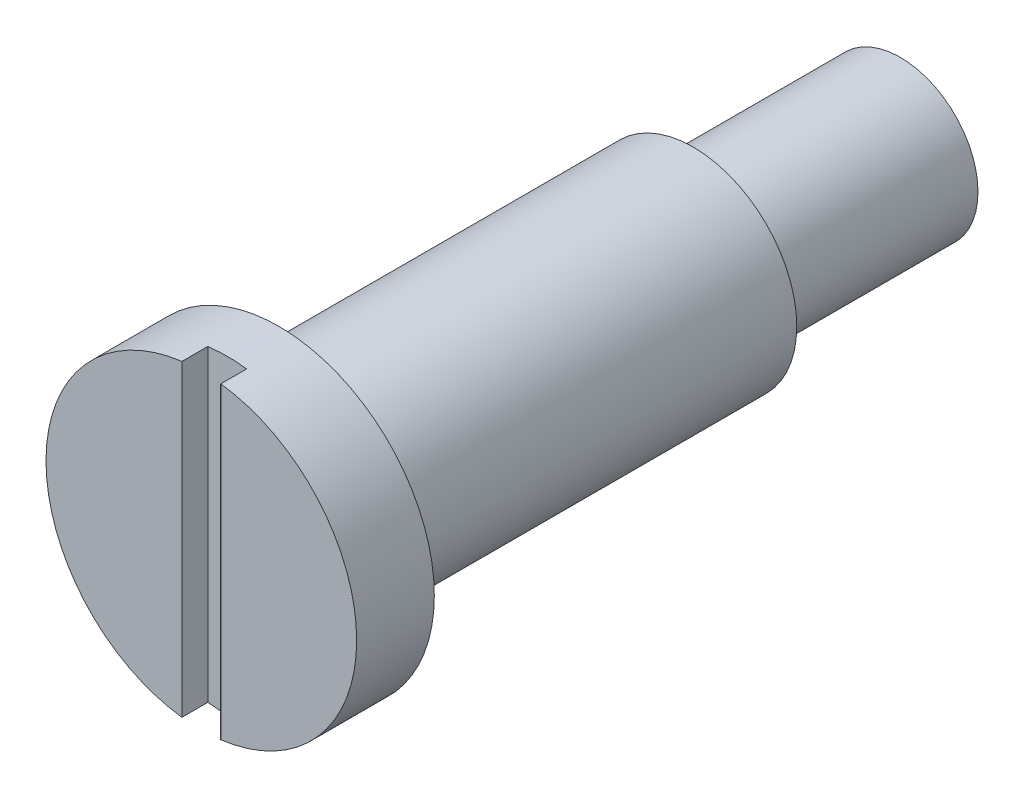
SolidWorks part; units mm, degrees
ref_plane "前视基准面" through (0, 0, 0) normal (0, 0, 1) x (1, 0, 0)
ref_plane "上视基准面" through (0, 0, 0) normal (0, 1, 0) x (1, 0, 0)
ref_plane "右视基准面" through (0, 0, 0) normal (1, 0, 0) x (0, 0, -1)
sketch "草图2" plane through (0, 0, 0) normal (1, 0, 0) x (0, 0, -1)
  line L0 (0, 0) -> (105.7683, 0) construction
  line L1 (0, 0) -> (0, 6)
  line L2 (0, 6) -> (3, 6)
  line L3 (3, 6) -> (3, 4)
  line L4 (3, 4) -> (19, 4)
  line L5 (19, 4) -> (19, 3)
  line L6 (0, 0) -> (27, 0)
  line L7 (19, 3) -> (27, 3)
  line L8 (27, 3) -> (27, 0)
  dimension "D1" = 12
  dimension "D2" = 16
  dimension "D3" = 3
  dimension "D4" = 8
  dimension "D5" = 6
  dimension "D6" = 8
revolve "旋转1" add sketch "草图2" angle 360 about L0
cosmetic thread "装饰螺纹线1"
sketch "草图3" plane through (0, 0, 0) normal (0, 0, 1) x (1, 0, 0)
  line L0 (0, 6) -> (0, -6) construction
  line L2 (-0.75, 6) -> (0.75, 6)
  line L3 (-0.75, 6) -> (-0.75, -6)
  line L4 (-0.75, -6) -> (0.75, -6)
  line L5 (0.75, 6) -> (0.75, -6)
  circle A0 centre (0, 0) radius 6 construction
  dimension "D1" = 1.5
extrude "切除-拉伸1" cut sketch "草图3" against normal blind 1
